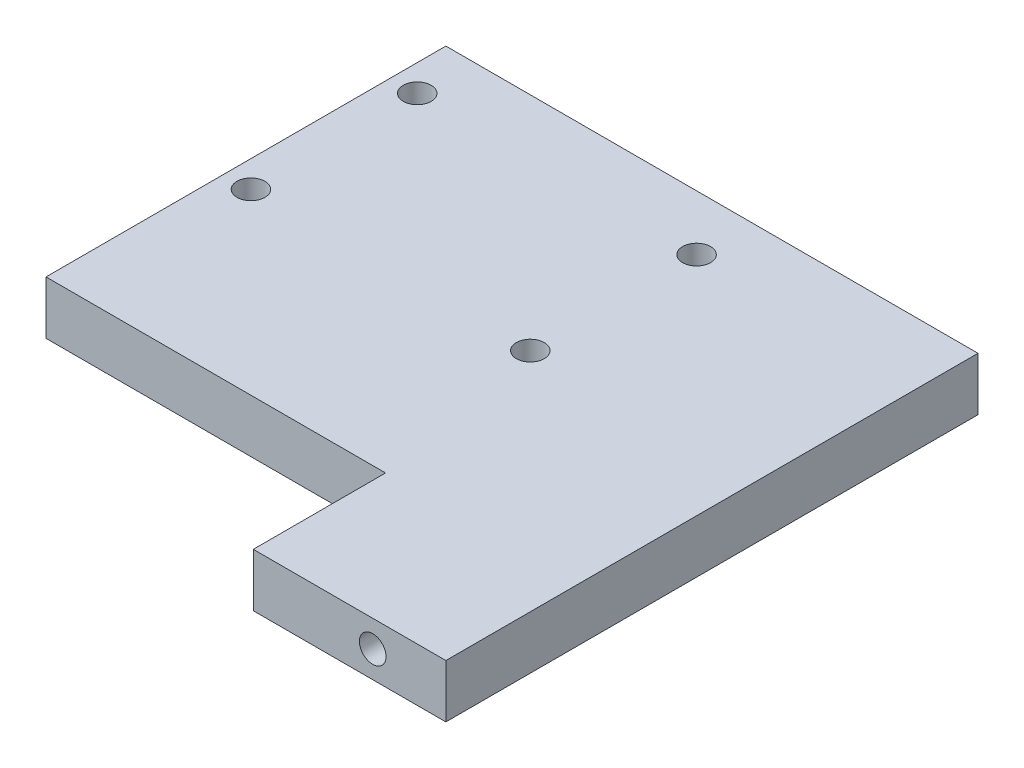
SolidWorks part; units mm, degrees
ref_plane "Front Plane" through (0, 0, 0) normal (0, 0, 1) x (1, 0, 0)
ref_plane "Top Plane" through (0, 0, 0) normal (0, 1, 0) x (1, 0, 0)
ref_plane "Right Plane" through (0, 0, 0) normal (1, 0, 0) x (0, 0, -1)
sketch "Sketch1" plane through (0, 0, 0) normal (0, 1, 0) x (1, 0, 0)
  line L1 (-20, -20) -> (20, -20)
  line L2 (-20, -20) -> (-20, 20)
  line L3 (-20, 20) -> (20, 20)
  line L4 (20, -20) -> (20, 20)
  line L5 (-20, -20) -> (20, 20) construction
  line L6 (-20, 20) -> (20, -20) construction
  point P0 (0, 0)
extrude "Boss-Extrude1" add sketch "Sketch1" along normal blind 4
ref_plane "Plane1" through (0, 4, 0) normal (0, 1, 0) x (1, 0, 0)
ref_plane "Plane2" through (0, 0, -20) normal (0, 0, -1) x (-1, 0, 0)
sketch "Sketch4" plane through (0, 0, 20) normal (0, 0, 1) x (1, 0, 0)
  line L0 (-20, 2) -> (-14.5, 2) construction
  line L1 (-20, 4) -> (-20, 0) construction
  line L2 (20, 2) -> (14.5, 2) construction
  line L3 (20, 4) -> (20, 0) construction
  circle A0 centre (-14.5, 2) radius 1
  circle A1 centre (14.5, 2) radius 1
extrude "Cut-Extrude2" cut sketch "Sketch4" against normal blind 2
sketch "Sketch5" plane through (0, 0, -20) normal (0, 0, -1) x (-1, 0, 0)
  line L0 (-20, 2) -> (-14.5, 2) construction
  line L1 (-20, 4) -> (-20, 0) construction
  line L2 (20, 2) -> (14.5, 2) construction
  line L3 (20, 4) -> (20, 0) construction
  circle A0 centre (-14.5, 2) radius 1
  circle A1 centre (14.5, 2) radius 1
extrude "Cut-Extrude3" cut sketch "Sketch5" against normal blind 2
ref_plane "Plane3" through (0, 0, 0) normal (0, -1, 0) x (-1, 0, 0)
sketch "Sketch6" plane through (0, 0, 0) normal (0, -1, 0) x (-1, 0, 0)
  line L0 (-21.581, 0) -> (21.581, 0) construction
  line L1 (0, 28.2231) -> (0, -28.2231) construction
  line L2 (-5, 17.8472) -> (-2.9989, 15.8461) construction
  line L3 (-5, 0.1233) -> (-5, 17.8472)
  line L4 (20, 0.1233) -> (20, 17.8472)
  line L5 (-5, 17.8472) -> (20, 17.8472)
  line L6 (20, -267.9041) -> (20, 17.8472) construction
  line L7 (20, 17.8472) -> (17.9989, 15.8461) construction
  line L8 (-5, 17.8472) -> (-2.9989, 15.8461) construction
  line L9 (-2.9989, 15.8461) -> (-2.9989, 3.3461) construction
  line L10 (17.9989, 15.8461) -> (17.9989, 3.3461) construction
  line L11 (20, 20) -> (20, -20) construction
  line L13 (-5, 0.1233) -> (20, 0.1233)
  circle A0 centre (17.9989, 15.8461) radius 1.05
  circle A1 centre (-2.9989, 15.8461) radius 1.05
  circle A2 centre (-2.9989, 3.3461) radius 1.05
  circle A3 centre (17.9989, 3.3461) radius 1.05
  point P0 (-3.4386, 0)
  point P4 (0, 0)
  point P7 (0, 0)
  point P9 (17.9989, 16.2927)
  point P24 (17.868, 15.8461)
extrude "Boss-Extrude3" add sketch "Sketch6" along normal blind 1
sketch "Sketch8" plane through (0, -1, 0) normal (0, -1, 0) x (1, 0, 0)
  circle A0 centre (-17.9989, -15.8461) radius 1.05
  circle A1 centre (2.9989, -15.8461) radius 1.05
  circle A2 centre (2.9989, -3.3461) radius 1.05
  circle A3 centre (-17.9989, -3.3461) radius 1.05
extrude "Cut-Extrude4" cut sketch "Sketch8" against normal through all
sketch "Sketch9" plane through (0, 0, 0) normal (0, -1, 0) x (-1, 0, 0)
  line L0 (20, -0.0583) -> (20, -10.0583) construction
  line L1 (20, 0.1233) -> (20, -20) construction
  line L3 (20, -10.0583) -> (-5.5238, -10.0583)
  line L4 (20, -10.0583) -> (20, -20)
  line L5 (20, -20) -> (-5.5238, -20)
  line L6 (-5.5238, -10.0583) -> (-5.5238, -20)
  line L7 (20, -20) -> (-20, -20) construction
  point P7 (-5.5238, -20)
extrude "Cut-Extrude5" cut sketch "Sketch9" against normal through all
